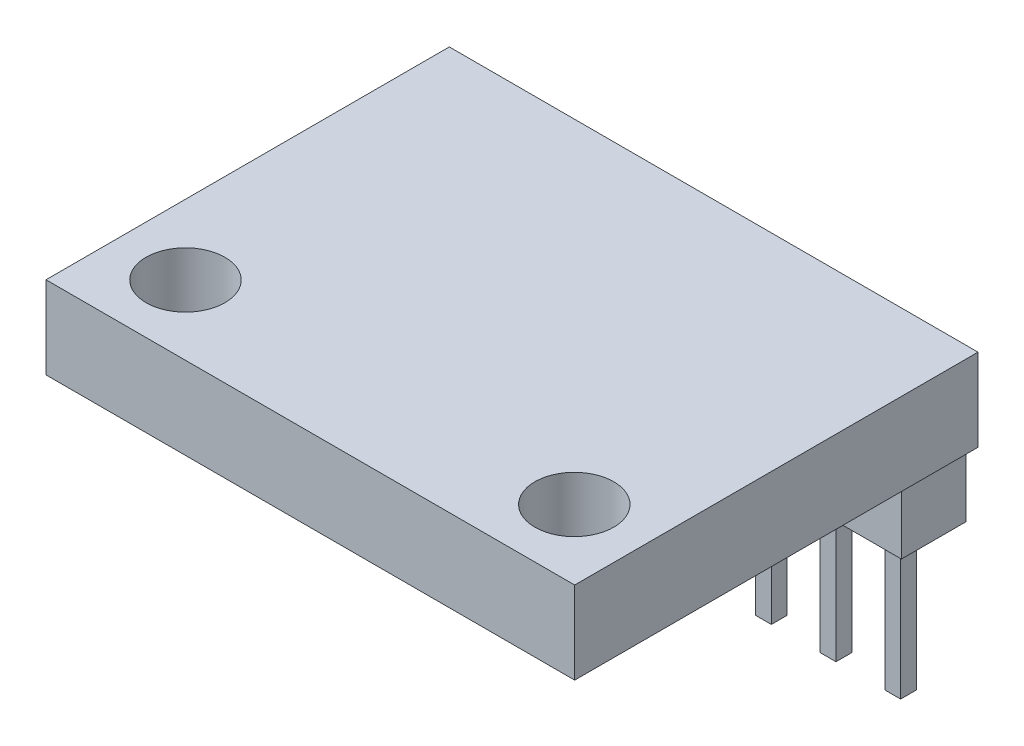
SolidWorks part; units mm, degrees
ref_plane "Front Plane" through (0, 0, 0) normal (0, 0, 1) x (1, 0, 0)
ref_plane "Top Plane" through (0, 0, 0) normal (0, 1, 0) x (1, 0, 0)
ref_plane "Right Plane" through (0, 0, 0) normal (1, 0, 0) x (0, 0, -1)
sketch "Sketch1" plane through (0, 0, 0) normal (0, 1, 0) x (1, 0, 0)
  line L0 (0, -8.7173) -> (0, 8.7173) construction
  line L1 (-1.9939, 1.9939) -> (1.9939, 1.9939) construction
  line L2 (-1.9939, 1.9939) -> (-1.9939, -1.9939) construction
  line L3 (-1.9939, -1.9939) -> (1.9939, -1.9939) construction
  line L4 (1.9939, 1.9939) -> (1.9939, -1.9939) construction
  line L5 (-1.9939, 1.9939) -> (1.9939, -1.9939) construction
  line L6 (-1.9939, -1.9939) -> (1.9939, 1.9939) construction
  line L7 (-10.3886, 8.6487) -> (10.3886, 8.6487)
  line L8 (-10.3886, 8.6487) -> (-10.3886, -7.2009)
  line L9 (-10.3886, -7.2009) -> (10.3886, -7.2009)
  line L10 (10.3886, 8.6487) -> (10.3886, -7.2009)
  line L11 (-10.3886, 8.6487) -> (10.3886, -7.2009) construction
  line L12 (-10.3886, -7.2009) -> (10.3886, 8.6487) construction
  circle A0 centre (7.6403, -4.4679) radius 1.5494
  circle A1 centre (-7.6403, -4.4679) radius 1.5494
  point P0 (0, 0)
  point P6 (0, 0.7239)
  point P15 (9.1897, -4.4679)
  point P16 (7.6403, -6.0173)
  dimension "D8" = 3.0988
  dimension "D1" = 3.9878
  dimension "D2" = 3.9878
  dimension "D3" = 9.1948
  dimension "D4" = 15.8496
  dimension "D5" = 20.7772
  dimension "D6" = 1.1836
  dimension "D7" = 1.1989
extrude "Boss-Extrude2" add sketch "Sketch1" along normal blind 3.2385
sketch "Sketch2" plane through (0, 0, 0) normal (0, 1, 0) x (1, 0, 0)
  line L0 (0, -1.7812) -> (0, 1.7812) construction
  line L1 (-10.2489, 5.7785) -> (10.2489, 5.7785)
  line L2 (-10.2489, 5.7785) -> (-10.2489, 8.3185)
  line L3 (-10.2489, 8.3185) -> (10.2489, 8.3185)
  line L4 (10.2489, 5.7785) -> (10.2489, 8.3185)
  line L5 (-10.2489, 5.7785) -> (10.2489, 8.3185) construction
  line L6 (-10.2489, 8.3185) -> (10.2489, 5.7785) construction
  line L7 (10.3886, 8.6487) -> (-10.3886, 8.6487) construction
  point P0 (0, 7.0485)
  dimension "D1" = 0.3302
  dimension "D2" = 20.4978
  dimension "D3" = 2.54
extrude "Boss-Extrude3" add sketch "Sketch2" against normal blind 2.4384
sketch "Sketch3" plane through (0, -2.4384, 0) normal (0, -1, 0) x (1, 0, 0)
  line L0 (-10.2489, -7.0485) -> (10.2489, -7.0485) construction
  line L1 (-10.2489, -8.3185) -> (-10.2489, -5.7785) construction
  line L2 (10.2489, -5.7785) -> (10.2489, -8.3185) construction
  line L3 (-6.604, -6.7374) -> (-6.604, -7.3597)
  line L4 (-9.144, -6.7374) -> (-8.5217, -6.7374)
  line L5 (-9.144, -6.7374) -> (-9.144, -7.3597)
  line L6 (-9.144, -7.3597) -> (-8.5217, -7.3597)
  line L7 (-8.5217, -6.7374) -> (-8.5217, -7.3597)
  line L8 (-9.144, -6.7374) -> (-8.5217, -7.3597) construction
  line L9 (-9.144, -7.3597) -> (-8.5217, -6.7374) construction
  line L10 (-6.604, -6.7374) -> (-5.9817, -6.7374)
  line L11 (-5.9817, -6.7374) -> (-5.9817, -7.3597)
  line L12 (-6.604, -7.3597) -> (-5.9817, -7.3597)
  line L13 (-4.064, -6.7374) -> (-4.064, -7.3597)
  line L14 (-4.064, -6.7374) -> (-3.4417, -6.7374)
  line L15 (-3.4417, -6.7374) -> (-3.4417, -7.3597)
  line L16 (-4.064, -7.3597) -> (-3.4417, -7.3597)
  line L17 (-1.524, -6.7374) -> (-1.524, -7.3597)
  line L18 (-1.524, -6.7374) -> (-0.9017, -6.7374)
  line L19 (-0.9017, -6.7374) -> (-0.9017, -7.3597)
  line L20 (-1.524, -7.3597) -> (-0.9017, -7.3597)
  line L21 (1.016, -6.7374) -> (1.016, -7.3597)
  line L22 (1.016, -6.7374) -> (1.6383, -6.7374)
  line L23 (1.6383, -6.7374) -> (1.6383, -7.3597)
  line L24 (1.016, -7.3597) -> (1.6383, -7.3597)
  line L25 (3.556, -6.7374) -> (3.556, -7.3597)
  line L26 (3.556, -6.7374) -> (4.1783, -6.7374)
  line L27 (4.1783, -6.7374) -> (4.1783, -7.3597)
  line L28 (3.556, -7.3597) -> (4.1783, -7.3597)
  line L29 (6.096, -6.7374) -> (6.096, -7.3597)
  line L30 (6.096, -6.7374) -> (6.7183, -6.7374)
  line L31 (6.7183, -6.7374) -> (6.7183, -7.3597)
  line L32 (6.096, -7.3597) -> (6.7183, -7.3597)
  line L33 (8.636, -6.7374) -> (8.636, -7.3597)
  line L34 (8.636, -6.7374) -> (9.2583, -6.7374)
  line L35 (9.2583, -6.7374) -> (9.2583, -7.3597)
  line L36 (8.636, -7.3597) -> (9.2583, -7.3597)
  point P6 (-8.8329, -7.0485)
  dimension "D1" = 1.1049
  dimension "D2" = 0.6223
  dimension "D4" = 2.54
  dimension "D3" = 8
extrude "Boss-Extrude4" add sketch "Sketch3" along normal blind 5.7404
ref_plane "Plane1" through (0, 2.0383, 0) normal (0, 1, 0) x (1, 0, 0)
sketch "Sketch4" plane through (0, 2.0383, 0) normal (0, 1, 0) x (1, 0, 0)
  point P0 (0, 0)
